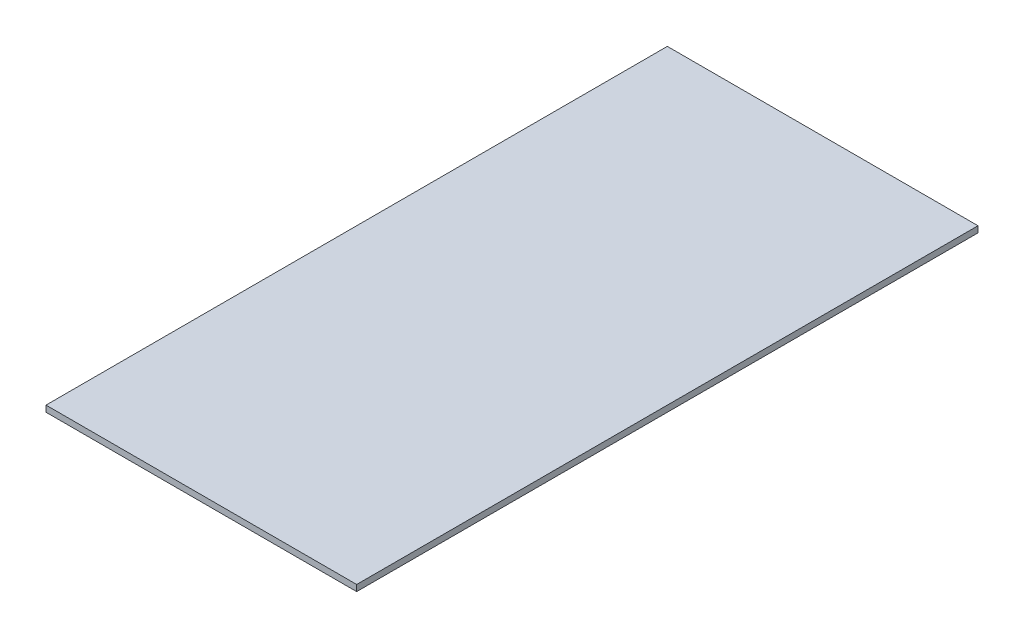
SolidWorks part; units mm, degrees
ref_plane "Front Plane" through (0, 0, 0) normal (0, 0, 1) x (1, 0, 0)
ref_plane "Top Plane" through (0, 0, 0) normal (0, 1, 0) x (1, 0, 0)
ref_plane "Right Plane" through (0, 0, 0) normal (1, 0, 0) x (0, 0, -1)
sketch "Sketch1" plane through (0, 0, 0) normal (0, 1, 0) x (1, 0, 0)
  line L1 (-100, -150.5113) -> (100, -150.5113)
  line L2 (-100, -150.5113) -> (-100, 249.4887)
  line L3 (-100, 249.4887) -> (100, 249.4887)
  line L4 (100, -150.5113) -> (100, 249.4887)
  line L5 (-100, -150.5113) -> (100, 249.4887) construction
  line L6 (-100, 249.4887) -> (100, -150.5113) construction
  point P1 (0, 49.4887)
  dimension "D1" = 400
  dimension "D2" = 200
extrude "Boss-Extrude1" add sketch "Sketch1" along normal blind 4
equation "\"m3_hole\"= 3.5"
equation "\"m3_washer\"= 7.3"
equation "\"m3_nut\"= 5.3"
equation "\"guide_width\"= 10.0"
equation "\"guide_diameter\"= 64.0"
equation "\"guide_tab_length\" = 10.0"
equation "\"guide_tab_width\" = 9.0"
equation "\"plywood_width\"= 4.0"
equation "\"D1@Boss-Extrude1\"=\"plywood_width\""
